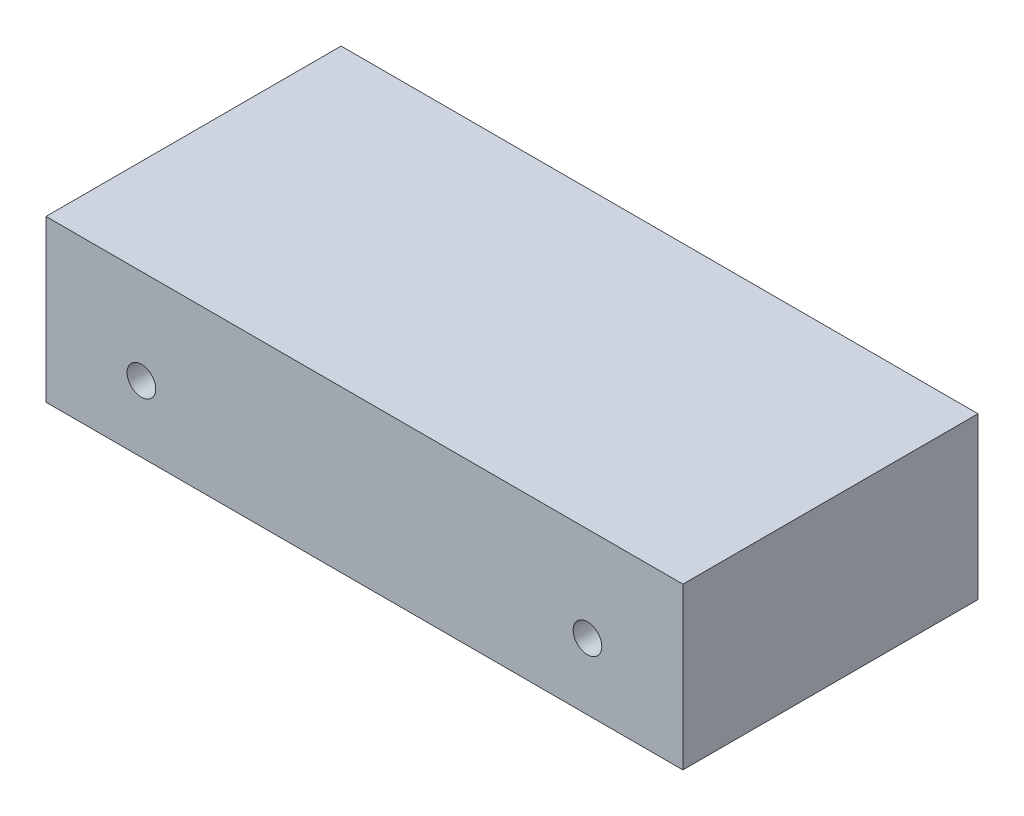
SolidWorks part; units mm, degrees
material "Custom Plastic"
ref_plane "X-Y Datum" through (0, 0, 0) normal (0, 0, 1) x (1, 0, 0)
ref_plane "X-Z Datum" through (0, 0, 0) normal (0, 1, 0) x (1, 0, 0)
ref_plane "Y-Z Datum" through (0, 0, 0) normal (1, 0, 0) x (0, 0, -1)
sketch "Sketch1" plane through (0, 0, 0) normal (0, 0, 1) x (1, 0, 0)
  line L1 (-155.321, 39.243) -> (155.321, 39.243)
  line L2 (-155.321, 39.243) -> (-155.321, -39.243)
  line L3 (-155.321, -39.243) -> (155.321, -39.243)
  line L4 (155.321, 39.243) -> (155.321, -39.243)
  line L5 (-155.321, 39.243) -> (155.321, -39.243) construction
  line L6 (-155.321, -39.243) -> (155.321, 39.243) construction
  point P0 (0, 0)
  dimension "D1" = 310.642
  dimension "D2" = 78.486
extrude "Boss-Extrude1" add sketch "Sketch1" along normal blind 143.9418
sketch "Sketch2" plane through (0, 0, 143.9418) normal (0, 0, 1) x (1, 0, 0)
  line L0 (-155.321, -39.243) -> (155.321, -39.243) construction
  line L1 (-155.321, 39.243) -> (-155.321, -39.243) construction
  circle A0 centre (-108.7882, -6.8834) radius 6.985
  circle A1 centre (108.7882, -6.8834) radius 6.985
  dimension "D3" = 13.97
  dimension "D1" = 32.3596
  dimension "D2" = 46.5328
  dimension "D4" = 217.5764
extrude "Cut-Extrude1" cut sketch "Sketch2" against normal blind 25.4
